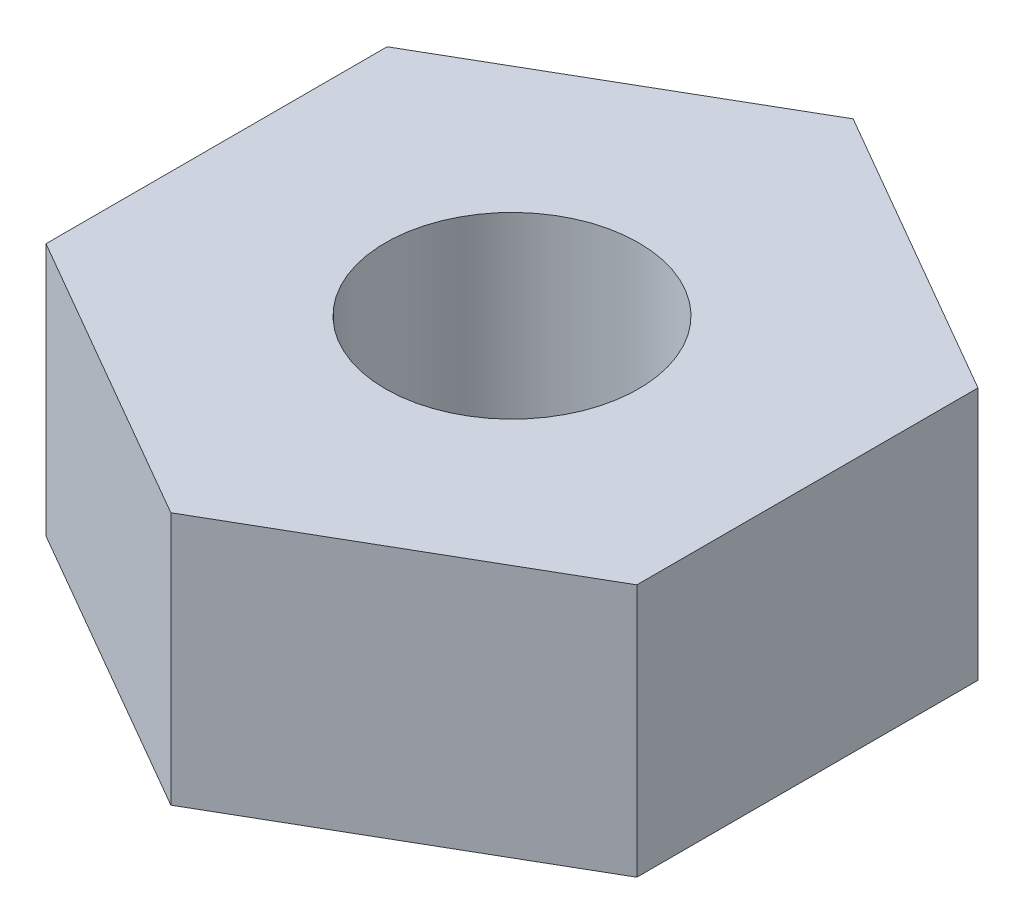
SolidWorks part; units mm, degrees
ref_plane "Alzado" through (0, 0, 0) normal (0, 0, 1) x (1, 0, 0)
ref_plane "Planta" through (0, 0, 0) normal (0, 1, 0) x (1, 0, 0)
ref_plane "Vista lateral" through (0, 0, 0) normal (1, 0, 0) x (0, 0, -1)
sketch "Croquis1" plane through (0, 0, 0) normal (0, 1, 0) x (1, 0, 0)
  line L1 (0, 4.0415) -> (-3.5, 2.0207)
  line L2 (-3.5, 2.0207) -> (-3.5, -2.0207)
  line L3 (-3.5, -2.0207) -> (0, -4.0415)
  line L4 (0, -4.0415) -> (3.5, -2.0207)
  line L5 (3.5, -2.0207) -> (3.5, 2.0207)
  line L6 (3.5, 2.0207) -> (0, 4.0415)
  circle A0 centre (0, 0) radius 3.5 construction
  dimension "D1" = 7
extrude "Saliente-Extruir1" add sketch "Croquis1" along normal blind 3
sketch "Croquis3" plane through (0, 3, 0) normal (0, 1, 0) x (1, 0, 0)
  circle A0 centre (0, 0) radius 1.5
  dimension "D1" = 3
extrude "Cortar-Extruir1" cut sketch "Croquis3" against normal blind 5.5
